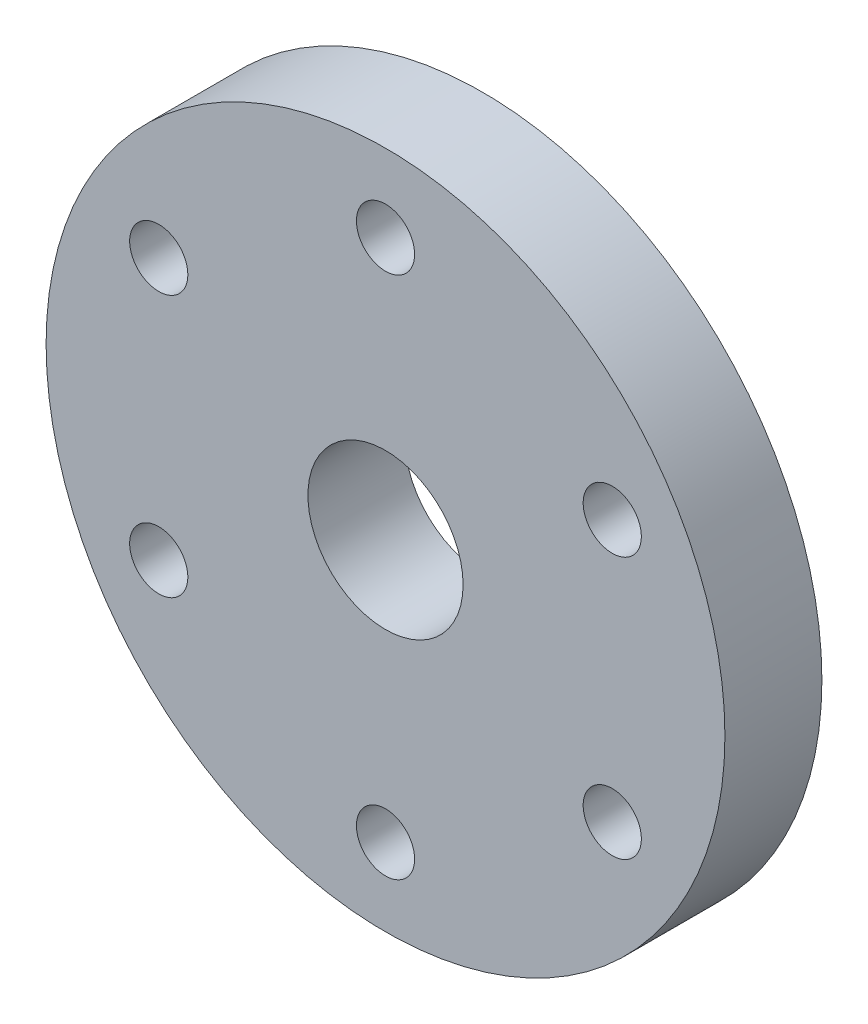
SolidWorks part; units mm, degrees
ref_plane "前视基准面" through (0, 0, 0) normal (0, 0, 1) x (1, 0, 0)
ref_plane "上视基准面" through (0, 0, 0) normal (0, 1, 0) x (1, 0, 0)
ref_plane "右视基准面" through (0, 0, 0) normal (1, 0, 0) x (0, 0, -1)
sketch "草图1" plane through (0, 0, 0) normal (0, 0, 1) x (1, 0, 0)
  circle A0 centre (0, 0) radius 17.5
  dimension "D1" = 35
extrude "凸台-拉伸1" add sketch "草图1" along normal blind 5
sketch "草图2" plane through (0, 0, 5) normal (0, 0, 1) x (1, 0, 0)
  circle A0 centre (0, 0) radius 13.5
  circle A1 centre (0, 13.5) radius 1.5
  circle A2 centre (11.6913, 6.75) radius 1.5
  circle A3 centre (11.6913, -6.75) radius 1.5
  circle A4 centre (0, 0) radius 4
  circle A5 centre (0, -13.5) radius 1.5
  circle A6 centre (-11.6913, -6.75) radius 1.5
  circle A7 centre (-11.6913, 6.75) radius 1.5
  point P11 (0, 0)
  dimension "D1" = 27
  dimension "D2" = 3
  dimension "D4" = 8
  dimension "D3" = 6
extrude "切除-拉伸1" cut sketch "草图2" against normal blind 5 contours A1 | A2 | A3 | A4 | A6 | A5 | A7
